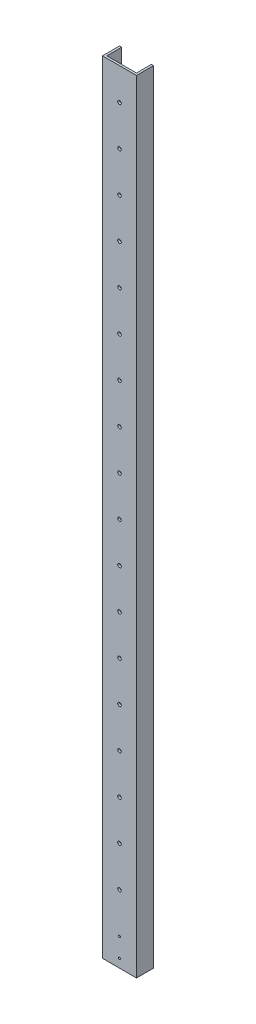
SolidWorks part; units mm, degrees
ref_plane "Front" through (0, 0, 0) normal (0, 0, 1) x (1, 0, 0)
ref_plane "Top" through (0, 0, 0) normal (0, 1, 0) x (1, 0, 0)
ref_plane "Right" through (0, 0, 0) normal (1, 0, 0) x (0, 0, -1)
sketch "Sketch1" plane through (0, 0, 0) normal (0, 1, 0) x (1, 0, 0)
  line L0 (3.175, 3.175) -> (3.175, 25.4)
  line L1 (0, 0) -> (50.8, 0)
  line L2 (0, 0) -> (0, 25.4)
  line L4 (50.8, 0) -> (50.8, 25.4)
  line L5 (3.175, 3.175) -> (47.625, 3.175)
  line L6 (47.625, 3.175) -> (47.625, 25.4)
  line L7 (0, 25.4) -> (3.175, 25.4)
  line L8 (50.8, 25.4) -> (47.625, 25.4)
  dimension "D1" = 25.4
  dimension "D2" = 50.8
  dimension "D3" = 3.175
extrude "Boss-Extrude1" add sketch "Sketch1" along normal blind 1168.4
sketch "Sketch2" plane through (0, 0, 0) normal (0, 0, 1) x (1, 0, 0)
  line L0 (25.4, 0) -> (25.4, 101.6) construction
  line L1 (0, 0) -> (50.8, 0) construction
  circle A0 centre (25.4, 101.6) radius 2.667
  circle A1 centre (25.4, 161.544) radius 2.667
  circle A2 centre (25.4, 221.488) radius 2.667
  circle A3 centre (25.4, 281.432) radius 2.667
  circle A4 centre (25.4, 341.376) radius 2.667
  circle A5 centre (25.4, 401.32) radius 2.667
  circle A6 centre (25.4, 461.264) radius 2.667
  circle A7 centre (25.4, 521.208) radius 2.667
  circle A8 centre (25.4, 581.152) radius 2.667
  circle A9 centre (25.4, 641.096) radius 2.667
  circle A10 centre (25.4, 701.04) radius 2.667
  circle A11 centre (25.4, 760.984) radius 2.667
  circle A12 centre (25.4, 820.928) radius 2.667
  circle A13 centre (25.4, 880.872) radius 2.667
  circle A14 centre (25.4, 940.816) radius 2.667
  circle A15 centre (25.4, 1000.76) radius 2.667
  circle A16 centre (25.4, 1060.704) radius 2.667
  circle A17 centre (25.4, 1120.648) radius 2.667
  dimension "D2" = 5.334
  dimension "D1" = 101.6
  dimension "D3" = 18
extrude "Cut-Extrude1" cut sketch "Sketch2" against normal up to next
sketch "Sketch4" plane through (0, 0, 0) normal (0, 0, 1) x (1, 0, 0)
  line L0 (25.4, 41.275) -> (50.8, 41.275) construction
  line L1 (50.8, 1168.4) -> (50.8, 0) construction
  line L2 (25.4, 41.275) -> (0, 41.275) construction
  line L3 (0, 1168.4) -> (0, 0) construction
  line L4 (25.4, 41.275) -> (25.4, 12.7) construction
  line L5 (25.4, 12.7) -> (25.4, 0) construction
  line L6 (0, 0) -> (50.8, 0) construction
  circle A1 centre (25.4, 41.275) radius 1.5875
  circle A3 centre (25.4, 12.7) radius 1.5875
  dimension "D1" = 28.575
  dimension "D2" = 12.7
extrude "Cut-Extrude2" cut sketch "Sketch4" against normal up to next
ref_plane "Mid_Plane" through (25.4, 0, 0) normal (1, 0, 0) x (0, 0, -1)
